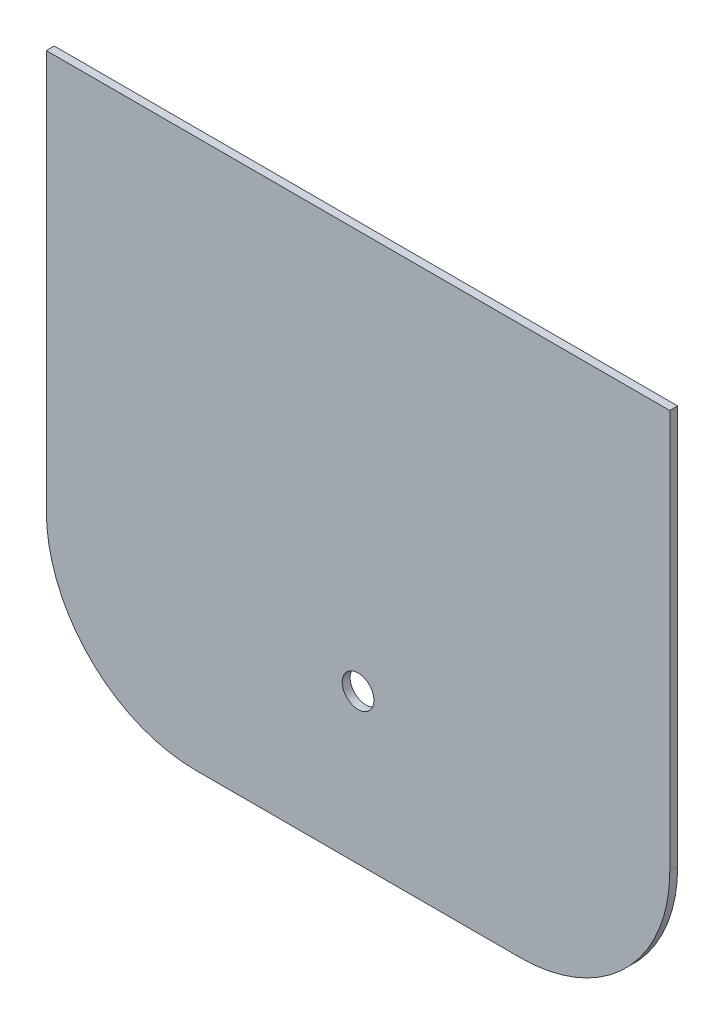
SolidWorks part; units mm, degrees
ref_plane "Alzado" through (0, 0, 0) normal (0, 0, 1) x (1, 0, 0)
ref_plane "Planta" through (0, 0, 0) normal (0, 1, 0) x (1, 0, 0)
ref_plane "Vista lateral" through (0, 0, 0) normal (1, 0, 0) x (0, 0, -1)
sketch "Croquis1" plane through (0, 0, 0) normal (0, 0, 1) x (1, 0, 0)
  line L1 (0, 0) -> (250, 0)
  line L2 (0, 0) -> (0, 220)
  line L3 (0, 220) -> (250, 220)
  line L4 (250, 0) -> (250, 220)
  dimension "D1" = 250
  dimension "D2" = 220
extrude "Saliente-Extruir1" add sketch "Croquis1" along normal blind 3.175
fillet "Redondeo1" radius 60 2 edges at (250, 0, 1.5875) (0, 0, 1.5875)
sketch "Croquis2" plane through (0, 0, 3.175) normal (0, 0, 1) x (1, 0, 0)
  line L0 (125, 0) -> (125, 60) construction
  line L1 (60, 0) -> (190, 0) construction
  circle A0 centre (125, 60) radius 6.35
  dimension "D2" = 12.7
  dimension "D1" = 60
extrude "Cortar-Extruir1" cut sketch "Croquis2" against normal blind 6.35
